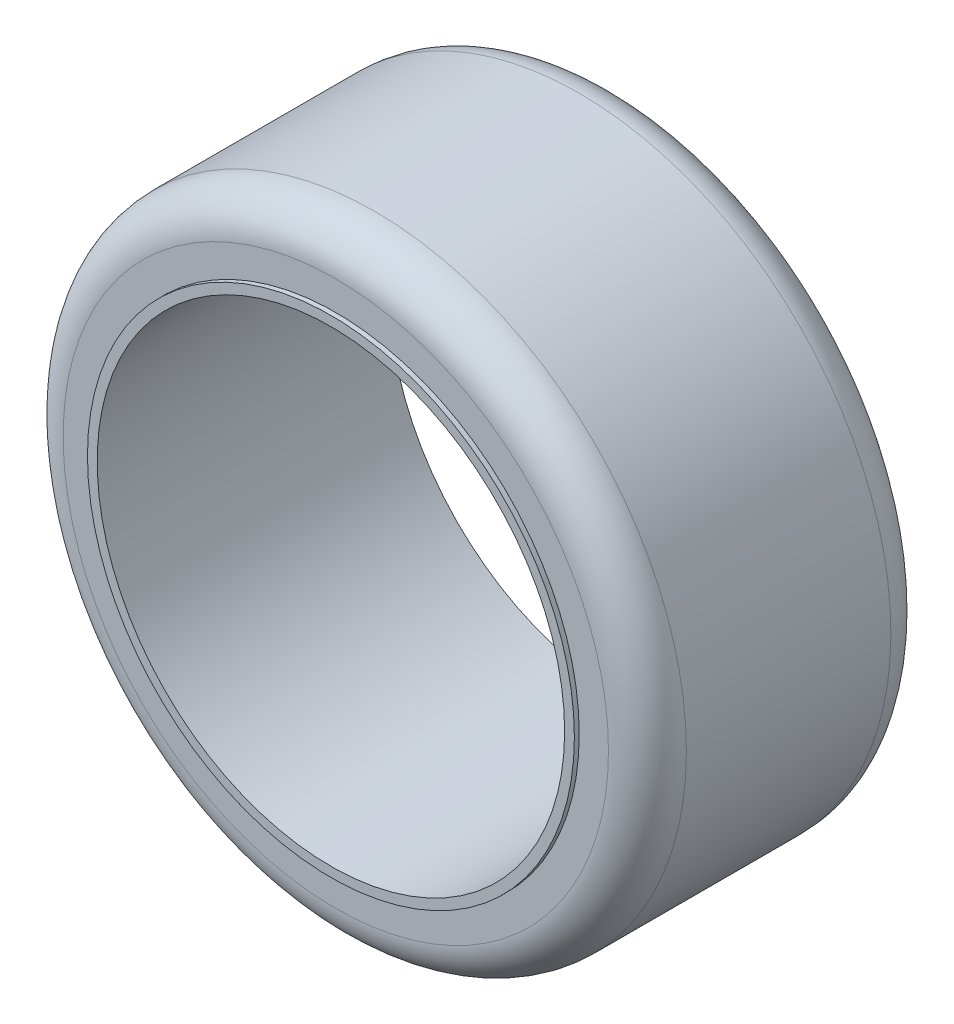
SolidWorks part; units mm, degrees
ref_plane "Front" through (0, 0, 0) normal (0, 0, 1) x (1, 0, 0)
ref_plane "Top" through (0, 0, 0) normal (0, 1, 0) x (1, 0, 0)
ref_plane "Right" through (0, 0, 0) normal (1, 0, 0) x (0, 0, -1)
sketch "Esquisse1" plane through (0, 0, 0) normal (0, 0, 1) x (1, 0, 0)
  circle A0 centre (0, 0) radius 24
  circle A1 centre (0, 0) radius 25
  dimension "D1" = 48
  dimension "D2" = 50
extrude "Boss.-Extru.1" add sketch "Esquisse1" along normal blind 30
sketch "Esquisse2" plane through (0, 0, 30) normal (0, 0, 1) x (1, 0, 0)
  circle A0 centre (0, 0) radius 32
  circle M2 centre (0, 0) radius 25
  dimension "D1" = 64
extrude "Boss.-Extru.2" add sketch "Esquisse2" against normal blind 30 contours A0 M2
sketch "Esquisse3" plane through (0, 0, 30) normal (0, 0, 1) x (1, 0, 0)
  circle A0 centre (0, 0) radius 25
  dimension "D1" = 50
extrude "Enlèv. de mat.-Extru.-Mince1" cut sketch "Esquisse3" against normal blind 0.5 thin
ref_plane "Plan1" through (0, 0, 15) normal (0, 0, 1) x (1, 0, 0)
mirror "Symétrie1" about plane through (0, 0, 15) normal (0, 0, 1) of "Enlèv. de mat.-Extru.-Mince1"
fillet "Congé1" radius 4 2 edges at (32, 0, 0.5) (32, 0, 29.5)
